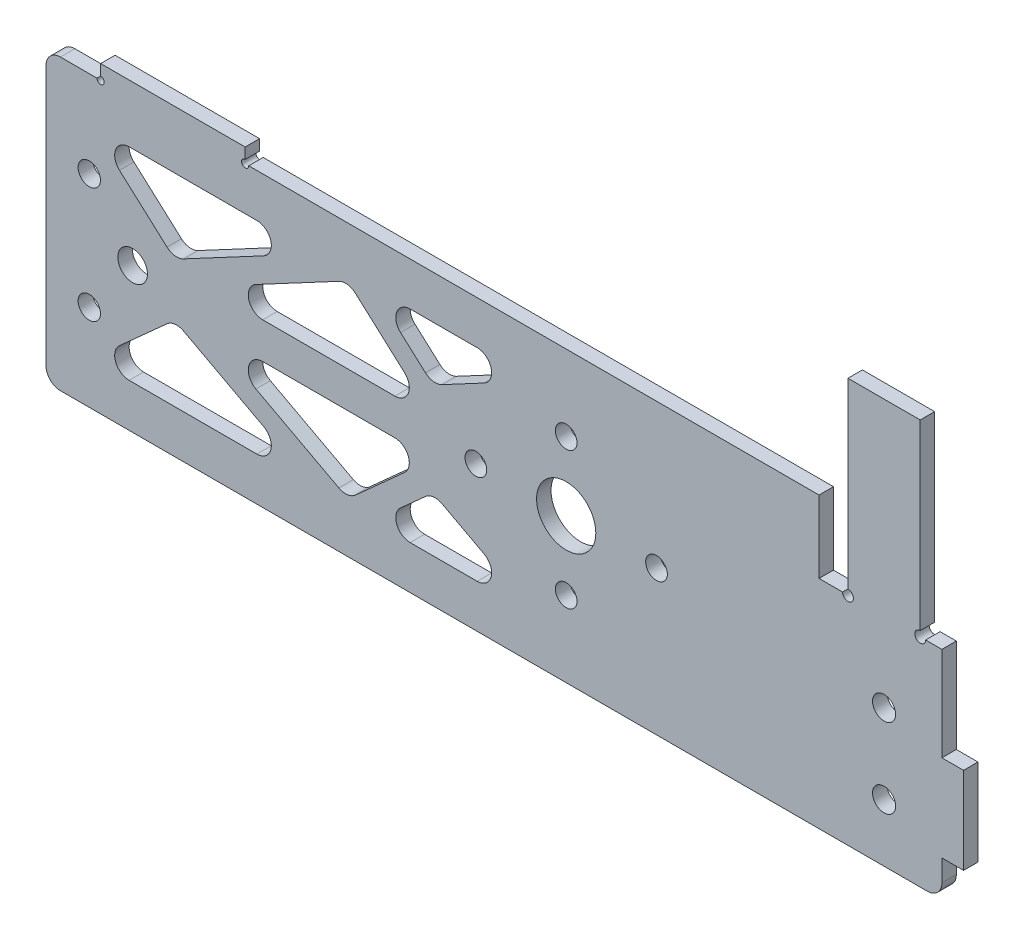
SolidWorks part; units mm, degrees
material "Thornel Mat VMA"
ref_plane "前视基准面" through (0, 0, 0) normal (0, 0, 1) x (1, 0, 0)
ref_plane "上视基准面" through (0, 0, 0) normal (0, 1, 0) x (1, 0, 0)
ref_plane "右视基准面" through (0, 0, 0) normal (1, 0, 0) x (0, 0, -1)
sketch "草图1" plane through (0, 0, 0) normal (0, 0, 1) x (1, 0, 0)
  line L1 (0, 0) -> (17, 0)
  line L2 (0, 0) -> (0, 54)
  line L3 (0, 54) -> (17, 54)
  line L4 (20, 5) -> (20, 17)
  line L7 (20, 5) -> (17, 5)
  line L8 (17, 0) -> (17, 5)
  line L11 (20, 17) -> (17, 17)
  line L12 (17, 54) -> (17, 17)
  point P11 (18.5, 5)
  dimension "D1" = 54
  dimension "D2" = 17
  dimension "D3" = 17
  dimension "D4" = 5
  dimension "D5" = 12
  dimension "D6" = 3
extrude "凸台-拉伸1" add sketch "草图1" along normal blind 2
sketch "草图2" plane through (0, 0, 2) normal (0, 0, 1) x (1, 0, 0)
  line L0 (0, 0) -> (17, 0) construction
  line L1 (0, 54) -> (0, 0) construction
  circle A0 centre (9, 8) radius 1.6
  circle A1 centre (9, 19) radius 1.6
  dimension "D1" = 3.2
  dimension "D2" = 3.2
  dimension "D3" = 8
  dimension "D4" = 9
  dimension "D5" = 11
  dimension "D6" = 9
extrude "切除-拉伸1" cut sketch "草图2" against normal through all
sketch "草图3" plane through (0, 0, 2) normal (0, 0, 1) x (1, 0, 0)
  line L0 (0, 0) -> (17, 0) construction
  line L1 (17, 54) -> (14, 54)
  line L2 (17, 54) -> (17, 30)
  line L3 (17, 30) -> (14, 30)
  line L4 (14, 54) -> (14, 30)
  line L6 (0, 54) -> (4, 54)
  line L7 (0, 54) -> (0, 30)
  line L8 (0, 30) -> (4, 30)
  line L9 (4, 54) -> (4, 30)
  dimension "D1" = 30
  dimension "D2" = 3
  dimension "D3" = 4
extrude "切除-拉伸2" cut sketch "草图3" against normal through all
sketch "草图4" plane through (0, 0, 2) normal (0, 0, 1) x (1, 0, 0)
  line L1 (20, 5) -> (17, 5)
  line L2 (20, 5) -> (20, 17)
  line L3 (20, 17) -> (17, 17)
  line L4 (17, 5) -> (17, 17)
extrude "切除-拉伸3" cut sketch "草图4" against normal through all
sketch "草图5" plane through (0, 0, 2) normal (0, 0, 1) x (1, 0, 0)
  line L0 (0, 30) -> (4, 30) construction
  line L1 (0, 0) -> (-83, 0)
  line L2 (0, 0) -> (0, 30)
  line L3 (0, 30) -> (-83, 30)
  line L4 (-83, 0) -> (-83, 30)
  dimension "D1" = 83
extrude "凸台-拉伸2" add sketch "草图5" against normal through all
sketch "草图6" plane through (0, 0, 2) normal (0, 0, 1) x (1, 0, 0)
  line L0 (-97.0935, 20) -> (17.0448, 20) construction
  line L1 (-83, 0) -> (17, 0) construction
  circle A0 centre (9, 19) radius 1.6 construction
  circle A1 centre (-35, 20) radius 4.1
  dimension "D1" = 20
  dimension "D2" = 8.2
  dimension "D3" = 44
extrude "切除-拉伸4" cut sketch "草图6" against normal through all
sketch "草图7" plane through (0, 0, 2) normal (0, 0, 1) x (1, 0, 0)
  line L0 (4, 30) -> (4, 54) construction
  line L1 (-83, 30) -> (0, 30)
  line L2 (-83, 30) -> (-83, 40)
  line L3 (-83, 40) -> (0, 40)
  line L4 (0, 30) -> (0, 40)
  dimension "D1" = 10
  dimension "D2" = 4
extrude "凸台-拉伸4" add sketch "草图7" against normal through all
sketch "草图8" plane through (0, 0, 2) normal (0, 0, 1) x (1, 0, 0)
  circle A0 centre (-35, 20) radius 9.5 construction
  circle A1 centre (-35, 20) radius 12.5 construction
  circle A2 centre (-35, 29.5) radius 1.5
  circle A3 centre (-35, 10.5) radius 1.5
  circle A4 centre (-47.5, 20) radius 1.5
  circle A5 centre (-22.5, 20) radius 1.5
  dimension "D1" = 19
  dimension "D2" = 25
  dimension "D3" = 3
extrude "切除-拉伸5" cut sketch "草图8" against normal blind 10
sketch "草图13" plane through (-83, 0, 0) normal (-1, 0, 0) x (0, 0, 1)
  line L0 (2, 40) -> (2, 0) construction
  line L1 (0, 0) -> (2, 0)
  line L2 (0, 0) -> (0, 40)
  line L3 (0, 40) -> (2, 40)
  line L4 (2, 0) -> (2, 40)
  line L5 (0, 40) -> (2, 40) construction
extrude "凸台-拉伸6" add sketch "草图13" along normal blind 24
sketch "草图16" plane through (0, 0, 0) normal (0, 0, -1) x (-1, 0, 0)
  circle A0 centre (-4, 30) radius 0.75
  circle A1 centre (-14, 30) radius 0.75
  dimension "D1" = 1.5
  dimension "D2" = 1.5
extrude "切除-拉伸9" cut sketch "草图16" against normal blind 3
sketch "草图17" plane through (0, 54, 0) normal (0, 1, 0) x (1, 0, 0)
  line L1 (14, -2) -> (4, -2)
  line L2 (14, -2) -> (14, 0)
  line L3 (14, 0) -> (4, 0)
  line L4 (4, -2) -> (4, 0)
extrude "凸台-拉伸8" add sketch "草图17" along normal blind 2
sketch "草图18" plane through (0, 0, 2) normal (0, 0, 1) x (1, 0, 0)
  line L0 (-99.4394, 40) -> (-99.4394, 42)
  line L1 (0, 40) -> (-107, 40) construction
  line L2 (-99.4394, 42) -> (-79.4394, 42)
  line L3 (-79.4394, 42) -> (-79.4394, 40)
  line L4 (-79.4394, 40) -> (-99.4394, 40)
  line L8 (-104.4394, 40) -> (-104.4394, 42) construction
  line L9 (-99.4394, 40) -> (-79.4394, 40)
  line M14 (0, 40) -> (-107, 40)
  dimension "D1" = 2
  dimension "D2" = 5
  dimension "D3" = 20
extrude "凸台-拉伸9" add sketch "草图18" against normal blind 2 contours L3 L2 L0 M14
sketch "草图19" plane through (0, 0, 2) normal (0, 0, 1) x (1, 0, 0)
  circle A0 centre (-101.0094, 12) radius 1.55
  circle A1 centre (-101.0094, 28) radius 1.55 construction
  circle A2 centre (-95.0094, 20) radius 2.05 construction
  circle A3 centre (-101.0094, 28) radius 1.55
  circle A4 centre (-95.0094, 20) radius 2.05
  dimension "D1" = 3.1
  dimension "D2" = 8
extrude "切除-拉伸10" cut sketch "草图19" against normal blind 10
fillet "圆角1" radius 2 3 edges at (-107, 40, 1) (-107, 0, 1) (17, 0, 1)
sketch "草图21" plane through (0, 0, 0) normal (0, 0, -1) x (-1, 0, 0)
  line L0 (100.7125, 6) -> (89.2095, 16.3387)
  line L1 (89.2095, 16.3387) -> (69.8072, 6)
  line L2 (69.8072, 6) -> (100.7125, 6)
  line L3 (65.2279, 6.9592) -> (85.0094, 17.5)
  line L4 (85.0094, 17.5) -> (53.5, 17.5)
  line L5 (53.5, 17.5) -> (65.2279, 6.9592)
  line L6 (61.8072, 6) -> (53.4351, 13.5247)
  line L7 (53.4351, 13.5247) -> (39.3138, 6)
  line L8 (39.3138, 6) -> (61.8072, 6)
  line L9 (105, 0) -> (-15, 0) construction
  line L10 (107, 20) -> (-17, 20) construction
  line L11 (107, 38) -> (107, 2) construction
  line L12 (-17, 2) -> (-17, 30) construction
  line L13 (53.4351, 26.4753) -> (39.3138, 34)
  line L14 (61.8072, 34) -> (53.4351, 26.4753)
  line L15 (39.3138, 34) -> (61.8072, 34)
  line L16 (85.0094, 22.5) -> (53.5, 22.5)
  line L17 (65.2279, 33.0408) -> (85.0094, 22.5)
  line L18 (53.5, 22.5) -> (65.2279, 33.0408)
  line L19 (89.2095, 23.6613) -> (69.8072, 34)
  line L20 (100.7125, 34) -> (89.2095, 23.6613)
  line L21 (69.8072, 34) -> (100.7125, 34)
  circle A0 centre (95.0094, 20) radius 2.05 construction
  circle A1 centre (47.5, 20) radius 1.5 construction
  circle A2 centre (101.0094, 12) radius 1.55 construction
  circle A3 centre (35, 10.5) radius 1.5 construction
  dimension "D1" = 6
  dimension "D2" = 3
  dimension "D3" = 3
  dimension "D4" = 8
  dimension "D5" = 5
  dimension "D6" = 10
  dimension "D7" = 6
  dimension "D8" = 110
  dimension "D9" = 4.6609
  dimension "D10" = 6
extrude "切除-拉伸11" cut sketch "草图21" against normal blind 10
fillet "圆角2" radius 2 18 edges at (-69.8072, 34, 1) (-100.7125, 34, 1) (-89.2095, 23.6613, 1) (-39.3138, 34, 1) (-61.8072, 34, 1) (-53.4351, 26.4753, 1) (-53.5, 22.5, 1) (-65.2279, 33.0408, 1) (-85.0094, 22.5, 1) (-85.0094, 17.5, 1) (-65.2279, 6.9592, 1) (-53.5, 17.5, 1) (-53.4351, 13.5247, 1) (-39.3138, 6, 1) (-61.8072, 6, 1) (-89.2095, 16.3387, 1) (-69.8072, 6, 1) (-100.7125, 6, 1)
sketch "草图22" plane through (0, 0, 2) normal (0, 0, 1) x (1, 0, 0)
  line L0 (17, 2) -> (17, 30) construction
  line L1 (20, 17) -> (17, 17)
  line L2 (20, 17) -> (20, 5)
  line L3 (20, 5) -> (17, 5)
  line L4 (17, 17) -> (17, 5)
  line L5 (20, 17) -> (17, 5) construction
  line L6 (20, 5) -> (17, 17) construction
  line L7 (-105, 0) -> (15, 0) construction
  point P0 (18.5, 11)
  dimension "D1" = 5
  dimension "D2" = 3
  dimension "D3" = 12
extrude "凸台-拉伸10" add sketch "草图22" against normal blind 2
sketch "草图23" plane through (0, 0, 2) normal (0, 0, 1) x (1, 0, 0)
  circle A0 centre (-79.4394, 40) radius 0.5
  circle A1 centre (-99.4394, 40) radius 0.5
  dimension "D1" = 1
  dimension "D2" = 1
extrude "切除-拉伸12" cut sketch "草图23" against normal blind 10
